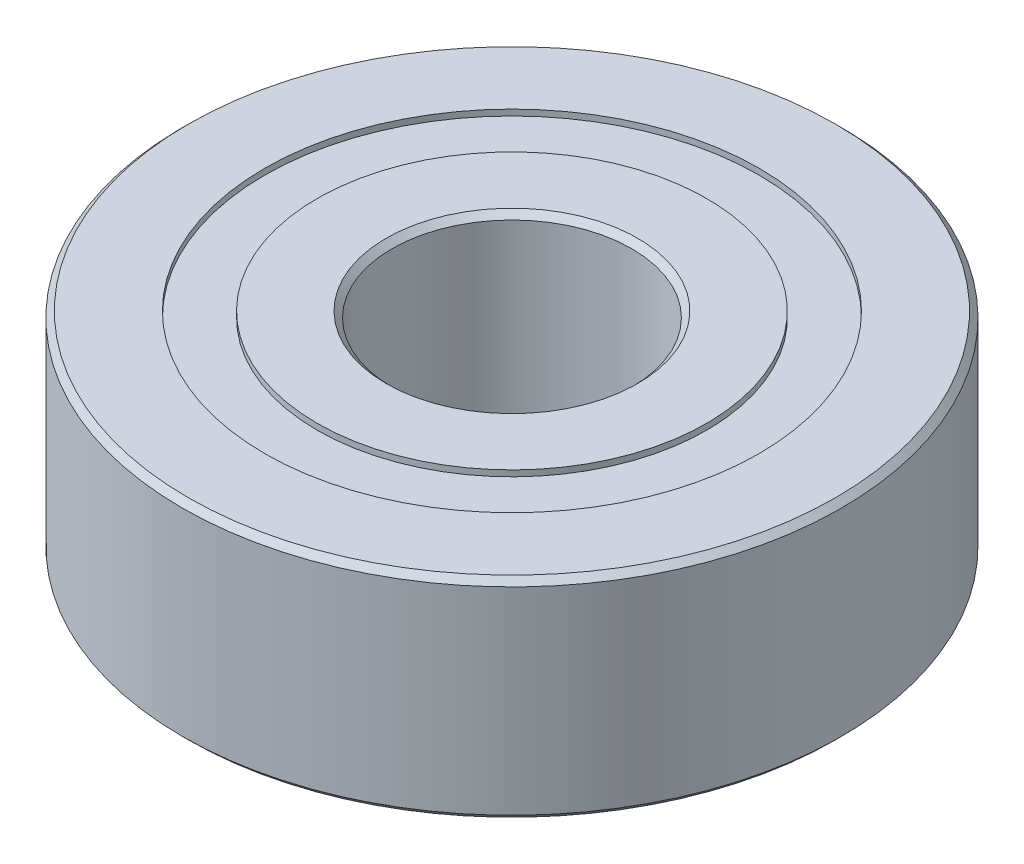
SolidWorks part; units mm, degrees
ref_plane "Front Plane" through (0, 0, 0) normal (0, 0, 1) x (1, 0, 0)
ref_plane "Top Plane" through (0, 0, 0) normal (0, 1, 0) x (1, 0, 0)
ref_plane "Right Plane" through (0, 0, 0) normal (1, 0, 0) x (0, 0, -1)
sketch "Sketch1" plane through (0, 0, 0) normal (0, 1, 0) x (1, 0, 0)
  circle A0 centre (0, 0) radius 11
  circle A1 centre (0, 0) radius 4
  dimension "D1" = 22
  dimension "D2" = 8
extrude "Boss-Extrude1" add sketch "Sketch1" along normal blind 7
sketch "Sketch2" plane through (0, 7, 0) normal (0, 1, 0) x (1, 0, 0)
  circle A0 centre (0, 0) radius 6.5
  circle A1 centre (0, 0) radius 8.25
  dimension "D1" = 16.5
  dimension "D2" = 13
extrude "Cut-Extrude1" cut sketch "Sketch2" against normal blind 0.2
sketch "Sketch3" plane through (0, 0, 0) normal (0, -1, 0) x (1, 0, 0)
  circle A0 centre (0, 0) radius 6.5 construction
  circle A1 centre (0, 0) radius 8.25
  circle A2 centre (0, 0) radius 8.25
  circle A3 centre (0, 0) radius 6.5
  dimension "D1" = 0
extrude "Cut-Extrude2" cut sketch "Sketch3" against normal blind 0.2
chamfer "Chamfer1" distance 0.2 angle 45 4 edges at (0, 7, 11) (0, 0, 11) (0, 7, 4) (0, 0, 4)
